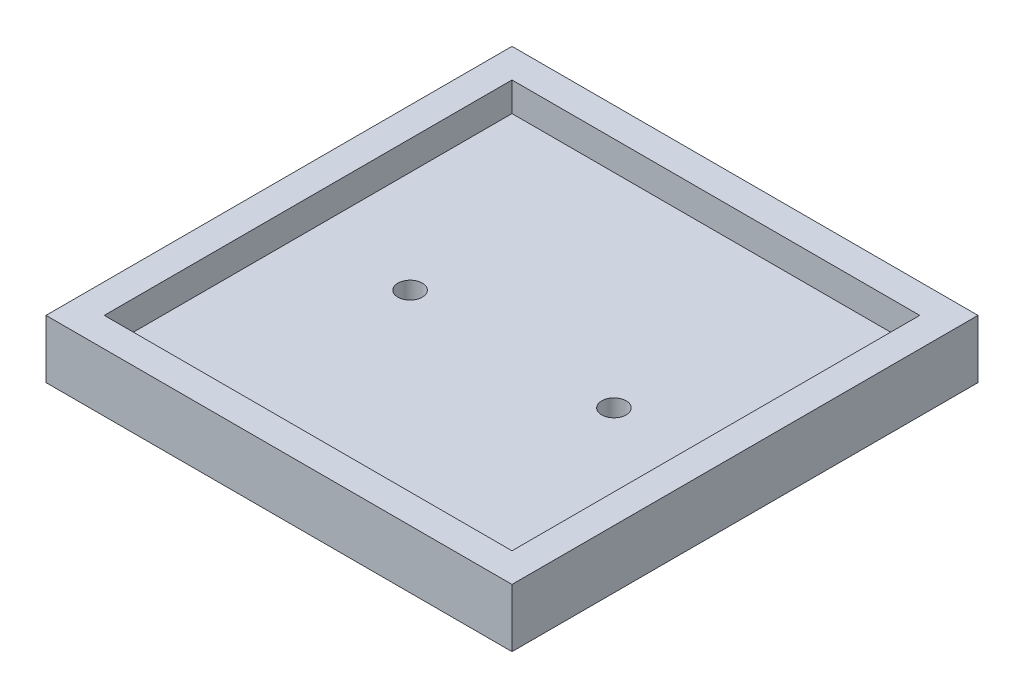
SolidWorks part; units mm, degrees
ref_plane "Front Plane" through (0, 0, 0) normal (0, 0, 1) x (1, 0, 0)
ref_plane "Top Plane" through (0, 0, 0) normal (0, 1, 0) x (1, 0, 0)
ref_plane "Right Plane" through (0, 0, 0) normal (1, 0, 0) x (0, 0, -1)
sketch "Sketch1" plane through (0, 0, 0) normal (0, 1, 0) x (1, 0, 0)
  line L1 (0, 0) -> (80, 0)
  line L2 (0, 0) -> (0, -80)
  line L3 (0, -80) -> (80, -80)
  line L4 (80, 0) -> (80, -80)
  point P4 (0, 0)
  dimension "D1" = 80
  dimension "D2" = 80
extrude "Boss-Extrude1" add sketch "Sketch1" along normal blind 5
sketch "Sketch2" plane through (0, 5, 0) normal (0, 1, 0) x (1, 0, 0)
  line L0 (80, 0) -> (0, 0) construction
  line L1 (5, -5) -> (75, -5)
  line L2 (5, -5) -> (5, -75)
  line L3 (5, -75) -> (75, -75)
  line L4 (75, -5) -> (75, -75)
  line L5 (0, 0) -> (0, -80) construction
  line L6 (0, -80) -> (80, -80) construction
  line L7 (80, -80) -> (80, 0) construction
  line L9 (0, 0) -> (80, 0)
  line L10 (0, 0) -> (0, -80)
  line L11 (0, -80) -> (80, -80)
  line L12 (80, 0) -> (80, -80)
  dimension "D1" = 5
  dimension "D2" = 5
  dimension "D3" = 5
  dimension "D4" = 5
extrude "Boss-Extrude2" add sketch "Sketch2" along normal blind 5
sketch "Sketch3" plane through (0, 5, 0) normal (0, 1, 0) x (1, 0, 0)
  line L0 (5, -5) -> (5, -75) construction
  line L1 (57.5, -40) -> (22.5, -40) construction
  line L2 (75, -5) -> (5, -5) construction
  circle A0 centre (22.5, -40) radius 2.1
  circle A1 centre (57.5, -40) radius 2.1
  point P4 (40, -40)
  point P9 (5, -40)
  point P10 (40, -5)
  dimension "D1" = 4.2
  dimension "D2" = 4.2
  dimension "D3" = 35
extrude "Cut-Extrude1" cut sketch "Sketch3" against normal up to next
